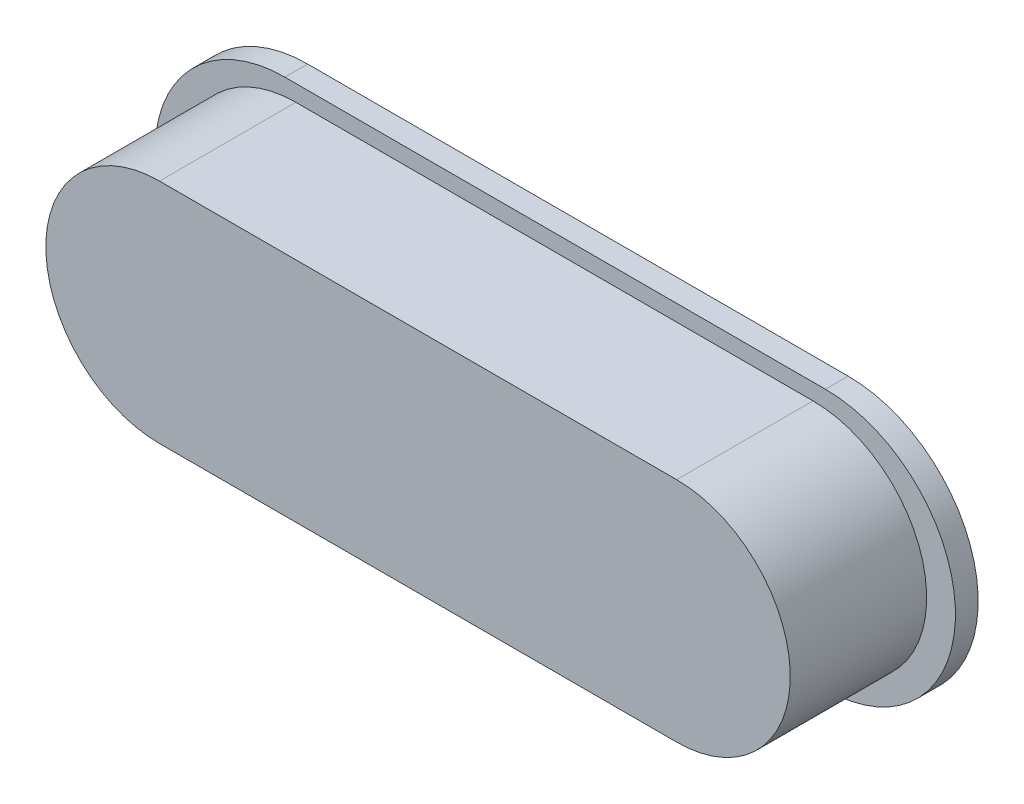
SolidWorks part; units mm, degrees
ref_plane "Płaszczyzna przednia" through (0, 0, 0) normal (0, 0, 1) x (1, 0, 0)
ref_plane "Płaszczyzna górna" through (0, 0, 0) normal (0, 1, 0) x (1, 0, 0)
ref_plane "Płaszczyzna prawa" through (0, 0, 0) normal (1, 0, 0) x (0, 0, -1)
sketch "Sketch1" plane through (0, 0, 0) normal (0, 0, 1) x (1, 0, 0)
  line L0 (-22.75, 0) -> (22.75, 0) construction
  line L5 (-22.75, 10) -> (22.75, 10)
  line L6 (-22.75, -10) -> (22.75, -10)
  arc A2 (-22.75, 10) -> (-22.75, -10) centre (-22.75, 0) ccw
  arc A3 (22.75, -10) -> (22.75, 10) centre (22.75, 0) ccw
  point P2 (0, 0)
  point P8 (-32.75, 0)
  point P9 (32.75, 0)
  dimension "D1" = 65.5
  dimension "D2" = 20
extrude "Boss-Extrude1" add sketch "Sketch1" along normal blind 12
sketch "Sketch2" plane through (0, 0, 0) normal (0, 0, 1) x (1, 0, 0)
  line L0 (-23.5, 0) -> (23.5, 0) construction
  line L1 (-23.5, 8) -> (23.5, 8)
  line L2 (-23.5, -8) -> (23.5, -8)
  arc A0 (-23.5, 8) -> (-23.5, -8) centre (-23.5, 0) ccw
  arc A1 (23.5, -8) -> (23.5, 8) centre (23.5, 0) ccw
  point P2 (0, 0)
  point P8 (31.5, 0)
  dimension "D1" = 16
  dimension "57" = 55
extrude "Cut-Extrude1" cut sketch "Sketch2" along normal blind 8
sketch "Sketch3" plane through (0, 0, 12) normal (0, 0, 1) x (1, 0, 0)
  line L0 (-22.75, 0) -> (23.5, 0) construction
  line L1 (-22.75, 8) -> (23.5, 8)
  line L2 (-22.75, -8) -> (23.5, -8)
  line L4 (-23.7171, 0) -> (23.8475, 0) construction
  line L5 (-23.7171, 11.4348) -> (23.8475, 11.4348)
  line L6 (-23.7171, -11.4348) -> (23.8475, -11.4348)
  line L7 (23.5, 8) -> (-23.5, 8) construction
  arc A0 (-22.75, 8) -> (-22.75, -8) centre (-22.75, 0) ccw
  arc A1 (23.5, -8) -> (23.5, 8) centre (23.5, 0) ccw
  arc A4 (-23.7171, 11.4348) -> (-23.7171, -11.4348) centre (-23.7171, 0) ccw
  arc A5 (23.8475, -11.4348) -> (23.8475, 11.4348) centre (23.8475, 0) ccw
  arc A6 (23.5, -8) -> (23.5, 8) centre (23.5, 0) ccw construction
  point P3 (0.375, 0)
  point P18 (0.0652, 0)
extrude "Boss-Extrude2" add sketch "Sketch3" against normal blind 2 from surface at -12 separate body starting at face at (0, 0, 0)
